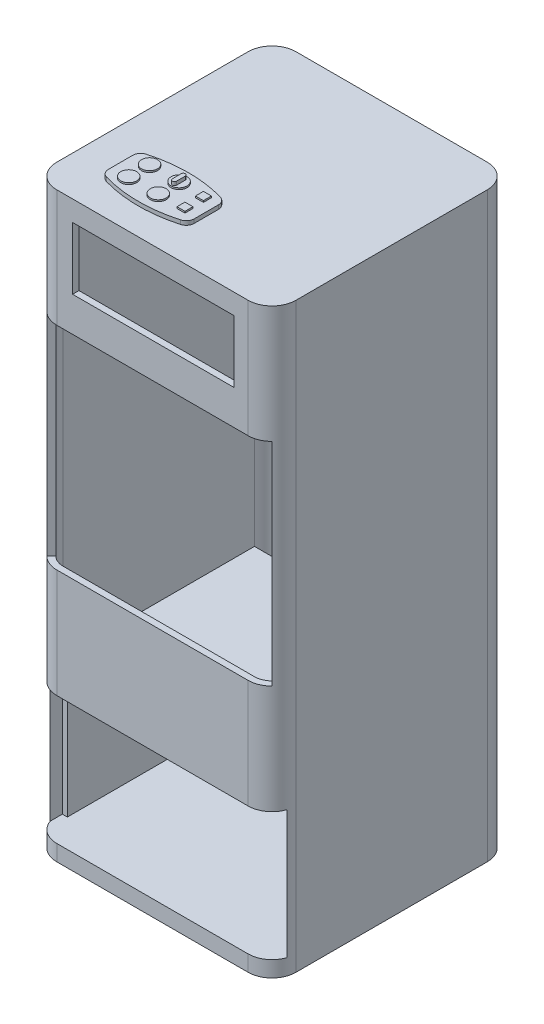
SolidWorks part; units mm, degrees
ref_plane "Front Plane" through (0, 0, 0) normal (0, 0, 1) x (1, 0, 0)
ref_plane "Top Plane" through (0, 0, 0) normal (0, 1, 0) x (1, 0, 0)
ref_plane "Right Plane" through (0, 0, 0) normal (1, 0, 0) x (0, 0, -1)
sketch "Sketch1" plane through (0, 0, 0) normal (0, 1, 0) x (1, 0, 0)
  line L1 (-335.5715, 336.2025) -> (45.4285, 336.2025)
  line L2 (-335.5715, 336.2025) -> (-335.5715, -44.7975)
  line L3 (-335.5715, -44.7975) -> (45.4285, -44.7975)
  line L4 (45.4285, 336.2025) -> (45.4285, -44.7975)
  dimension "D1" = 381
  dimension "D2" = 381
extrude "Boss-Extrude1" add sketch "Sketch1" along normal blind 25.4
sketch "Sketch2" plane through (0, 25.4, 0) normal (0, 1, 0) x (1, 0, 0)
  line L2 (-278.1898, 56.9099) -> (-278.1898, 18.2397)
  line L4 (-141.6075, 56.9099) -> (-141.6075, 18.2397)
  arc A0 (-268.9643, 69.1254) -> (-150.833, 69.1254) centre (-209.8987, -138.538) cw
  arc A1 (-268.9643, 6.0242) -> (-150.833, 6.0242) centre (-209.8987, 213.6876) ccw
  arc A2 (-278.1898, 18.2397) -> (-268.9643, 6.0242) centre (-265.4898, 18.2397) ccw
  arc A3 (-150.833, 6.0242) -> (-141.6075, 18.2397) centre (-154.3075, 18.2397) ccw
  arc A4 (-150.833, 69.1254) -> (-141.6075, 56.9099) centre (-154.3075, 56.9099) cw
  arc A5 (-268.9643, 69.1254) -> (-278.1898, 56.9099) centre (-265.4898, 56.9099) ccw
extrude "Boss-Extrude2" add sketch "Sketch2" along normal blind 6.35
sketch "Sketch3" plane through (0, 31.75, 0) normal (0, 1, 0) x (1, 0, 0)
  line L1 (-169.6021, 60.9159) -> (-156.9021, 60.9159)
  line L2 (-169.6021, 60.9159) -> (-169.6021, 48.2159)
  line L3 (-169.6021, 48.2159) -> (-156.9021, 48.2159)
  line L4 (-156.9021, 60.9159) -> (-156.9021, 48.2159)
  line L5 (-169.4881, 31.437) -> (-156.7881, 31.437)
  line L6 (-169.4881, 31.437) -> (-169.4881, 18.737)
  line L7 (-169.4881, 18.737) -> (-156.7881, 18.737)
  line L8 (-156.7881, 31.437) -> (-156.7881, 18.737)
  circle A0 centre (-249.9482, 55.4452) radius 12.7
  circle A1 centre (-249.9482, 22.3116) radius 12.7
  circle A2 centre (-202.8633, 55.4452) radius 12.7
  circle A3 centre (-202.8633, 22.3116) radius 12.7
  dimension "D1" = 25.4
  dimension "D2" = 25.4
  dimension "D3" = 25.4
  dimension "D4" = 25.4
  dimension "D5" = 12.7
  dimension "D6" = 12.7
  dimension "D7" = 12.7
  dimension "D8" = 12.7
extrude "Boss-Extrude3" add sketch "Sketch3" along normal blind 2.54
fillet "Fillet1" radius 38.1 4 edges at (-335.5715, 12.7, 44.7975) (45.4285, 12.7, 44.7975) (45.4285, 12.7, -336.2025) (-335.5715, 12.7, -336.2025)
sketch "Sketch6" plane through (0, 25.4, 0) normal (0, 1, 0) x (1, 0, 0)
  line L0 (7.3285, 326.0425) -> (-297.4715, 326.0425)
  line L1 (-325.4115, 298.1025) -> (-325.4115, -6.6975)
  line L2 (-297.4715, -34.6375) -> (7.3285, -34.6375)
  line L3 (35.2685, -6.6975) -> (35.2685, 298.1025)
  line L4 (-335.5715, 298.1025) -> (-335.5715, -6.6975)
  line L5 (-297.4715, -44.7975) -> (7.3285, -44.7975)
  line L6 (45.4285, -6.6975) -> (45.4285, 298.1025)
  line L7 (7.3285, 336.2025) -> (-297.4715, 336.2025)
  line L8 (-335.5715, 298.1025) -> (-335.5715, -6.6975)
  line L9 (-297.4715, -44.7975) -> (7.3285, -44.7975)
  line L10 (45.4285, -6.6975) -> (45.4285, 298.1025)
  line L11 (7.3285, 336.2025) -> (-297.4715, 336.2025)
  arc A0 (-297.4715, 326.0425) -> (-325.4115, 298.1025) centre (-297.4715, 298.1025) ccw
  arc A1 (-325.4115, -6.6975) -> (-297.4715, -34.6375) centre (-297.4715, -6.6975) ccw
  arc A2 (7.3285, -34.6375) -> (35.2685, -6.6975) centre (7.3285, -6.6975) ccw
  arc A3 (35.2685, 298.1025) -> (7.3285, 326.0425) centre (7.3285, 298.1025) ccw
  arc A4 (-335.5715, -6.6975) -> (-297.4715, -44.7975) centre (-297.4715, -6.6975) ccw
  arc A5 (7.3285, -44.7975) -> (45.4285, -6.6975) centre (7.3285, -6.6975) ccw
  arc A6 (45.4285, 298.1025) -> (7.3285, 336.2025) centre (7.3285, 298.1025) ccw
  arc A7 (-297.4715, 336.2025) -> (-335.5715, 298.1025) centre (-297.4715, 298.1025) ccw
  arc A8 (-335.5715, -6.6975) -> (-297.4715, -44.7975) centre (-297.4715, -6.6975) ccw
  arc A9 (7.3285, -44.7975) -> (45.4285, -6.6975) centre (7.3285, -6.6975) ccw
  arc A10 (45.4285, 298.1025) -> (7.3285, 336.2025) centre (7.3285, 298.1025) ccw
  arc A11 (-297.4715, 336.2025) -> (-335.5715, 298.1025) centre (-297.4715, 298.1025) ccw
  dimension "D1" = 0
  dimension "D2" = 10.16
extrude "Boss-Extrude4" add sketch "Sketch6" against normal blind 914.4
sketch "Sketch7" plane through (0, -889, 0) normal (0, -1, 0) x (1, 0, 0)
  line L4 (-297.4715, -336.2025) -> (7.3285, -336.2025)
  line L5 (45.4285, -298.1025) -> (45.4285, 6.6975)
  line L6 (7.3285, 44.7975) -> (-297.4715, 44.7975)
  line L7 (-335.5715, 6.6975) -> (-335.5715, -298.1025)
  line L8 (-297.4715, -336.2025) -> (7.3285, -336.2025)
  line L9 (45.4285, -298.1025) -> (45.4285, 6.6975)
  line L10 (7.3285, 44.7975) -> (-297.4715, 44.7975)
  line L11 (-335.5715, 6.6975) -> (-335.5715, -298.1025)
  arc A4 (-335.5715, -298.1025) -> (-297.4715, -336.2025) centre (-297.4715, -298.1025) ccw
  arc A5 (7.3285, -336.2025) -> (45.4285, -298.1025) centre (7.3285, -298.1025) ccw
  arc A6 (45.4285, 6.6975) -> (7.3285, 44.7975) centre (7.3285, 6.6975) ccw
  arc A7 (-297.4715, 44.7975) -> (-335.5715, 6.6975) centre (-297.4715, 6.6975) ccw
  arc A8 (-335.5715, -298.1025) -> (-297.4715, -336.2025) centre (-297.4715, -298.1025) ccw
  arc A9 (7.3285, -336.2025) -> (45.4285, -298.1025) centre (7.3285, -298.1025) ccw
  arc A10 (45.4285, 6.6975) -> (7.3285, 44.7975) centre (7.3285, 6.6975) ccw
  arc A11 (-297.4715, 44.7975) -> (-335.5715, 6.6975) centre (-297.4715, 6.6975) ccw
  dimension "D1" = 0
extrude "Boss-Extrude5" add sketch "Sketch7" along normal blind 12.7
sketch "Sketch9" plane through (0, 0, 0) normal (0, 0, 1) x (1, 0, 0)
  line L0 (7.3285, -901.7) -> (7.3285, 25.4) construction
  line L1 (-297.4715, 0) -> (7.3285, 0) construction
  line L2 (-297.4715, 0) -> (-297.4715, -76.2) construction
  line L3 (-297.4715, -76.2) -> (7.3285, -76.2) construction
  line L4 (7.3285, 0) -> (7.3285, -76.2) construction
  line L5 (45.4285, 25.4) -> (45.4285, -901.7) construction
  line L6 (-335.5715, -498.9803) -> (45.4285, -498.9803)
  line L7 (-335.5715, -498.9803) -> (-335.5715, -161.4197)
  line L8 (-335.5715, -161.4197) -> (45.4285, -161.4197)
  line L9 (45.4285, -498.9803) -> (45.4285, -161.4197)
  line L10 (-335.5715, -498.9803) -> (45.4285, -161.4197)
  line L11 (-335.5715, -161.4197) -> (45.4285, -498.9803)
  line L12 (-297.4715, 25.4) -> (7.3285, 25.4) construction
  circle A0 centre (-145.0715, -330.2) radius 152.4
  dimension "D1" = 76.2
  dimension "D2" = 254
  dimension "D3" = 25.4
extrude "Cut-Extrude2" cut sketch "Sketch9" along normal blind 167.894 contours A0 L10 L8 L11 | A0 L11 L7 L10 | A0 L11 L9 L10 | A0 L10 L6 L11 | L11 A0 L10 | L10 A0 L11 | L11 A0 L10 | L10 A0 L11
sketch "Sketch11" plane through (0, 0, -336.2025) normal (0, 0, -1) x (-1, 0, 0)
  line L0 (335.5715, -161.4197) -> (-45.4285, -161.4197) construction
  line L5 (335.5715, -498.9803) -> (-45.4285, -498.9803) construction
  line L6 (297.4715, -161.4197) -> (-7.3285, -161.4197)
  line L11 (297.4715, -498.9803) -> (-7.3285, -498.9803)
  line L12 (297.4715, -901.7) -> (297.4715, 25.4) construction
  line L13 (-7.3285, -161.4197) -> (297.4715, -161.4197)
  line L14 (-7.3285, -161.4197) -> (-7.3285, -498.9803)
  line L15 (-7.3285, -498.9803) -> (297.4715, -498.9803)
  line L16 (297.4715, -161.4197) -> (297.4715, -498.9803)
  circle A1 centre (145.0715, -330.2) radius 152.4
  arc A2 (42.9372, -217.088) -> (31.0021, -229.1361) centre (145.0715, -330.2) ccw
  dimension "D1" = 0
extrude "Cut-Extrude7" cut sketch "Sketch11" against normal blind 110.998
sketch "Sketch14" plane through (0, 0, 0) normal (0, 0, 1) x (1, 0, 0)
  line L1 (-333.3926, -876.3) -> (43.3314, -876.3)
  line L2 (-333.3926, -876.3) -> (-333.3926, -672.2669)
  line L3 (-333.3926, -672.2669) -> (43.3314, -672.2669)
  line L4 (43.3314, -876.3) -> (43.3314, -672.2669)
extrude "Cut-Extrude9" cut sketch "Sketch14" along normal blind 672.066
sketch "Sketch15" plane through (0, -889, 0) normal (0, 1, 0) x (1, 0, 0)
  line L4 (35.2685, -6.6975) -> (35.2685, 298.1025)
  line L5 (7.3285, 326.0425) -> (-297.4715, 326.0425)
  line L6 (-325.4115, 298.1025) -> (-325.4115, -6.6975)
  line L7 (-297.4715, -34.6375) -> (7.3285, -34.6375)
  line L8 (35.2685, -6.6975) -> (35.2685, 298.1025)
  line L9 (7.3285, 326.0425) -> (-297.4715, 326.0425)
  line L10 (-325.4115, 298.1025) -> (-325.4115, -6.6975)
  line L11 (-297.4715, -34.6375) -> (7.3285, -34.6375)
  arc A4 (7.3285, -34.6375) -> (35.2685, -6.6975) centre (7.3285, -6.6975) ccw
  arc A5 (35.2685, 298.1025) -> (7.3285, 326.0425) centre (7.3285, 298.1025) ccw
  arc A6 (-297.4715, 326.0425) -> (-325.4115, 298.1025) centre (-297.4715, 298.1025) ccw
  arc A7 (-325.4115, -6.6975) -> (-297.4715, -34.6375) centre (-297.4715, -6.6975) ccw
  arc A8 (7.3285, -34.6375) -> (35.2685, -6.6975) centre (7.3285, -6.6975) ccw
  arc A9 (35.2685, 298.1025) -> (7.3285, 326.0425) centre (7.3285, 298.1025) ccw
  arc A10 (-297.4715, 326.0425) -> (-325.4115, 298.1025) centre (-297.4715, 298.1025) ccw
  arc A11 (-325.4115, -6.6975) -> (-297.4715, -34.6375) centre (-297.4715, -6.6975) ccw
  dimension "D1" = 0
extrude "Boss-Extrude7" add sketch "Sketch15" along normal up to surface (12.7 mm away) up to face at (-145.0529, -876.3, 19.4885)
sketch "Sketch16" plane through (-325.4115, 0, 0) normal (1, 0, 0) x (0, 0, -1)
  line L0 (298.1025, -876.3) -> (298.1025, 0) construction
  line L1 (298.1025, -658.5703) -> (-6.6975, -658.5703)
  line L2 (298.1025, -658.5703) -> (298.1025, -651.9918)
  line L3 (298.1025, -651.9918) -> (-6.6975, -651.9918)
  line L4 (-6.6975, -658.5703) -> (-6.6975, -651.9918)
  line L5 (-6.6975, -672.2669) -> (-6.6975, -498.9803) construction
extrude "Boss-Extrude8" add sketch "Sketch16" along normal up to next
sketch "Sketch17" plane through (0, 0, 44.7975) normal (0, 0, 1) x (1, 0, 0)
  line L1 (-272.3249, -7.0302) -> (-15.3402, -7.0302)
  line L2 (-272.3249, -7.0302) -> (-272.3249, -106.148)
  line L3 (-272.3249, -106.148) -> (-15.3402, -106.148)
  line L4 (-15.3402, -7.0302) -> (-15.3402, -106.148)
  line L5 (-272.3249, -7.0302) -> (-15.3402, -106.148) construction
  line L6 (-272.3249, -106.148) -> (-15.3402, -7.0302) construction
  point P0 (-143.8326, -56.5891)
extrude "Cut-Extrude10" cut sketch "Sketch17" against normal blind 65.532
sketch "Sketch18" plane through (0, -498.9803, 0) normal (0, 1, 0) x (1, 0, 0)
  line L0 (34.2692, -33.6383) -> (27.085, -26.4541)
  line L1 (-324.4123, -33.6383) -> (-317.2281, -26.4541)
  line L8 (-297.4715, -44.7975) -> (7.3285, -44.7975)
  line L9 (45.4285, -6.6975) -> (45.4285, 0)
  line L10 (45.4285, 0) -> (35.2685, 0)
  line L11 (35.2685, 0) -> (35.2685, -6.6975)
  line L12 (7.3285, -34.6375) -> (-297.4715, -34.6375)
  line L13 (-325.4115, -6.6975) -> (-325.4115, 0)
  line L14 (-325.4115, 0) -> (-335.5715, 0)
  line L15 (-335.5715, 0) -> (-335.5715, -6.6975)
  line L16 (-297.4715, -44.7975) -> (7.3285, -44.7975)
  line L17 (45.4285, -6.6975) -> (45.4285, 0)
  line L18 (45.4285, 0) -> (35.2685, 0)
  line L19 (35.2685, 0) -> (35.2685, -6.6975)
  line L20 (7.3285, -34.6375) -> (-297.4715, -34.6375)
  line L21 (-325.4115, -6.6975) -> (-325.4115, 0)
  line L22 (-325.4115, 0) -> (-335.5715, 0)
  line L23 (-335.5715, 0) -> (-335.5715, -6.6975)
  arc A4 (7.3285, -44.7975) -> (45.4285, -6.6975) centre (7.3285, -6.6975) ccw
  arc A5 (7.3285, -34.6375) -> (35.2685, -6.6975) centre (7.3285, -6.6975) ccw
  arc A6 (-325.4115, -6.6975) -> (-297.4715, -34.6375) centre (-297.4715, -6.6975) ccw
  arc A7 (-335.5715, -6.6975) -> (-297.4715, -44.7975) centre (-297.4715, -6.6975) ccw
  arc A8 (7.3285, -44.7975) -> (45.4285, -6.6975) centre (7.3285, -6.6975) ccw
  arc A9 (7.3285, -34.6375) -> (35.2685, -6.6975) centre (7.3285, -6.6975) ccw
  arc A10 (-325.4115, -6.6975) -> (-297.4715, -34.6375) centre (-297.4715, -6.6975) ccw
  arc A11 (-335.5715, -6.6975) -> (-297.4715, -44.7975) centre (-297.4715, -6.6975) ccw
  arc M14 (7.3285, -44.7975) -> (45.4285, -6.6975) centre (7.3285, -6.6975) ccw
  line M15 (45.4285, -6.6975) -> (45.4285, 0)
  line M16 (45.4285, 0) -> (35.2685, 0)
  line M17 (35.2685, 0) -> (35.2685, -6.6975)
  arc M18 (35.2685, -6.6975) -> (7.3285, -34.6375) centre (7.3285, -6.6975) cw
  arc M20 (-297.4715, -34.6375) -> (-325.4115, -6.6975) centre (-297.4715, -6.6975) cw
  line M21 (-325.4115, -6.6975) -> (-325.4115, 0)
  line M22 (-325.4115, 0) -> (-335.5715, 0)
  line M23 (-335.5715, 0) -> (-335.5715, -6.6975)
  arc M24 (-335.5715, -6.6975) -> (-297.4715, -44.7975) centre (-297.4715, -6.6975) ccw
  dimension "D1" = 0
extrude "Boss-Extrude9" add sketch "Sketch18" along normal up to surface (337.5607 mm away) contours L1 M24 M20 M21 M22 M23 | L0 M14 M15 M16 M17 M18 up to face at (-145.0715, -161.4197, 17.7512)
sketch "Sketch19" plane through (0, 34.29, 0) normal (0, 1, 0) x (1, 0, 0)
  line L0 (-202.811, 61.9811) -> (-202.811, 47.9266) construction
  line L1 (-199.5251, 61.9811) -> (-199.5251, 47.9266)
  line L2 (-206.0969, 61.9811) -> (-206.0969, 47.9266)
  arc A0 (-199.5251, 61.9811) -> (-206.0969, 61.9811) centre (-202.811, 61.9811) ccw
  arc A1 (-206.0969, 47.9266) -> (-199.5251, 47.9266) centre (-202.811, 47.9266) ccw
  point P2 (-202.811, 54.9539)
extrude "Boss-Extrude10" add sketch "Sketch19" along normal blind 5.588
